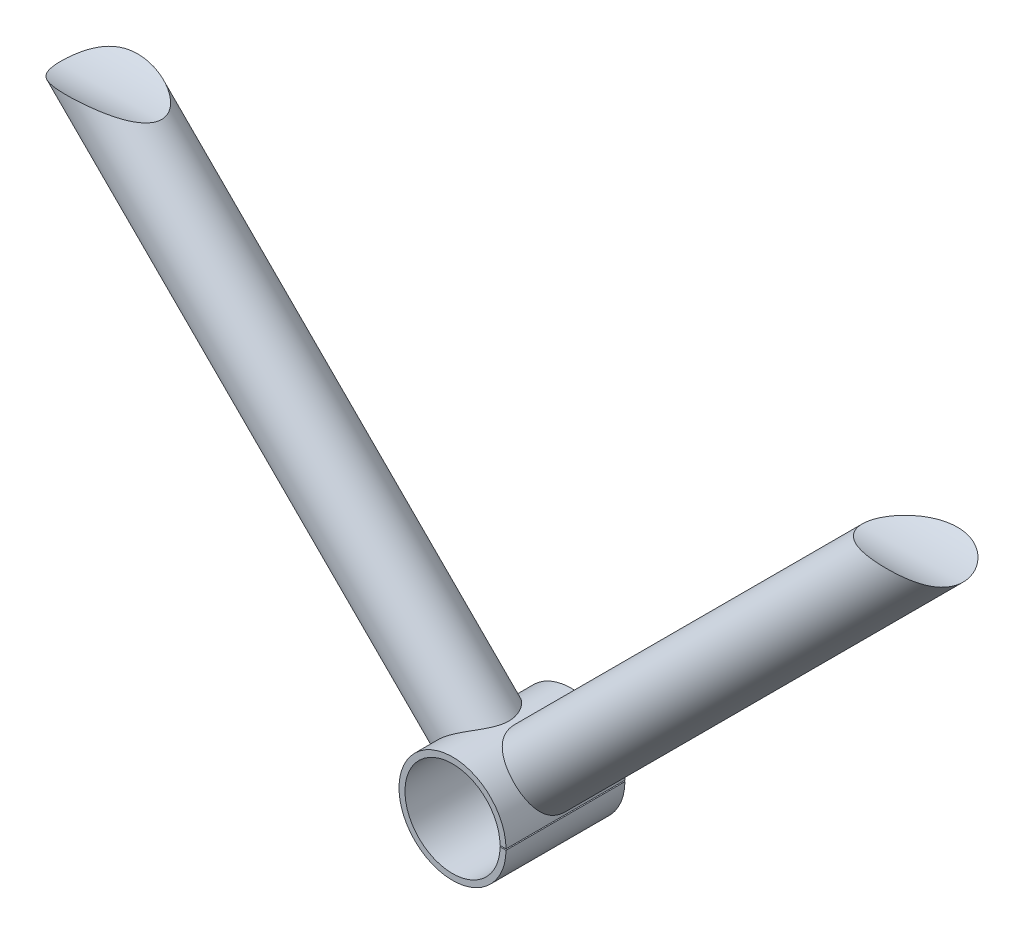
SolidWorks part; units mm, degrees
ref_plane "Front Plane" through (0, 0, 0) normal (0, 0, 1) x (1, 0, 0)
ref_plane "Top Plane" through (0, 0, 0) normal (0, 1, 0) x (1, 0, 0)
ref_plane "Right Plane" through (0, 0, 0) normal (1, 0, 0) x (0, 0, -1)
sketch "Sketch1" plane through (0, 0, 0) normal (0, 0, 1) x (1, 0, 0)
  line L1 (0, 0) -> (76.3087, 0)
  line L2 (0, 0) -> (0, 1.9255)
  line L3 (0, 1.9255) -> (76.3087, 1.9255)
  line L4 (76.3087, 0) -> (76.3087, 1.9255)
sketch "Sketch9" plane through (0, 0, 0) normal (0, 0, 1) x (1, 0, 0)
  circle A0 centre (0, 0) radius 8
  circle A1 centre (0, 0) radius 9
  dimension "D1" = 16
  dimension "D2" = 18
extrude "Boss-Extrude1" add sketch "Sketch9" along normal blind 20
sketch "Sketch10" plane through (0, 0, 20) normal (0, 0, 1) x (1, 0, 0)
  line L1 (10.4675, 0.1) -> (5.5325, 0.1)
  line L2 (10.4675, 0.1) -> (10.4675, -0.1)
  line L3 (10.4675, -0.1) -> (5.5325, -0.1)
  line L4 (5.5325, 0.1) -> (5.5325, -0.1)
  line L5 (10.4675, 0.1) -> (5.5325, -0.1) construction
  line L6 (10.4675, -0.1) -> (5.5325, 0.1) construction
  circle A0 centre (0, 0) radius 8 construction
  point P0 (8, 0)
  dimension "D1" = 0.2
extrude "Cut-Extrude1" cut sketch "Sketch10" against normal blind 20
ref_plane "Plane1" through (-6.364, 6.364, 0) normal (-0.7071, 0.7071, 0) x (0, 0, -1)
sketch "Sketch11" plane through (-6.364, 6.364, 0) normal (-0.7071, 0.7071, 0) x (0, 0, -1)
  line L0 (0, -9) -> (0, 9) construction
  circle A0 centre (-10, 0) radius 6
  dimension "D1" = 12
  dimension "D2" = 10
extrude "Boss-Extrude2" add sketch "Sketch11" along normal blind 100 and the other way up to surface
ref_plane "Plane2" through (6.364, 6.364, 0) normal (0.7071, 0.7071, 0) x (0, 0, -1)
sketch "Sketch12" plane through (6.364, 6.364, 0) normal (0.7071, 0.7071, 0) x (0, 0, -1)
  line L0 (0, -9) -> (0, 9) construction
  circle A0 centre (-10, 0) radius 6
  dimension "D1" = 12
  dimension "D2" = 10
extrude "Boss-Extrude3" add sketch "Sketch12" along normal blind 100 and the other way up to surface
sketch "Sketch14" plane through (0, 0, 0) normal (1, 0, 0) x (0, 0, -1)
  circle A0 centre (-10, 79.9) radius 12.5
  dimension "D1" = 25
  dimension "D2" = 80
extrude "Cut-Extrude3" cut sketch "Sketch14" against normal through all and the other way through all
sketch "Bend-Lines1" [suppressed] plane through (0, 0, 0) normal (0, 1, 0) x (1, 0, 0)
sketch "Bounding-Box1" [suppressed] plane through (0, 0, 0) normal (0, 1, 0) x (1, 0, 0)
